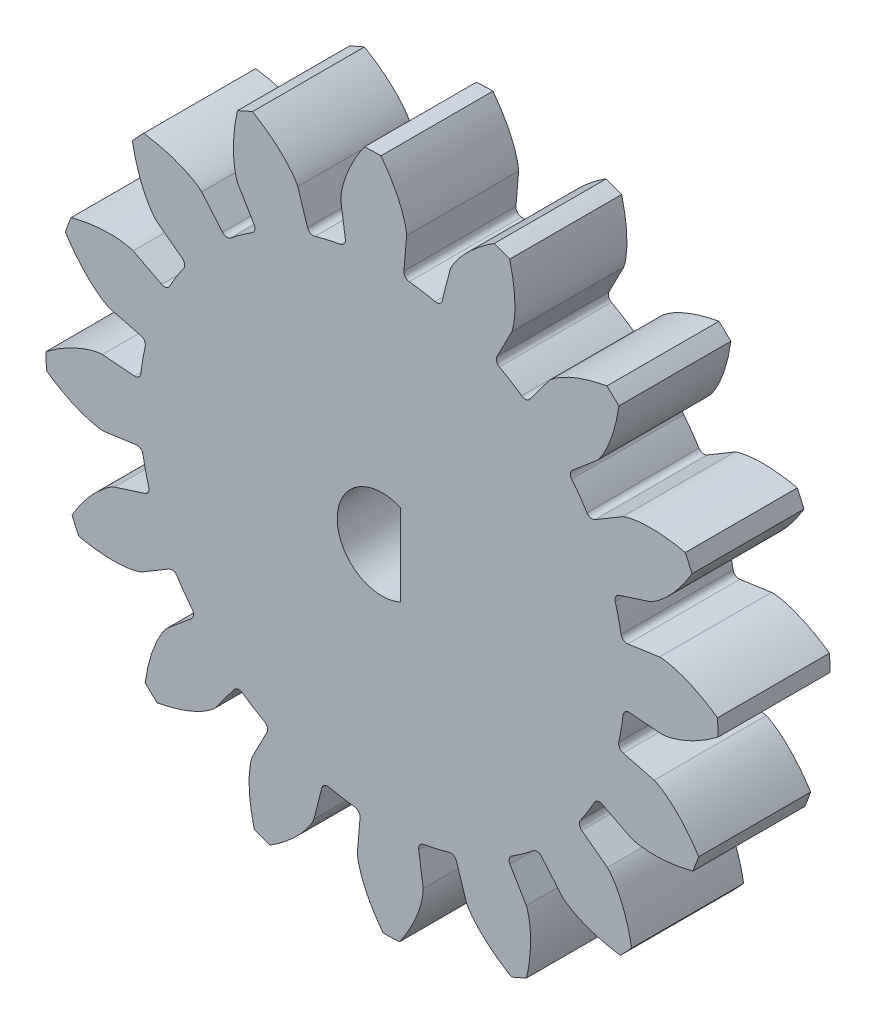
SolidWorks part; units mm, degrees
ref_plane "Front Plane" through (0, 0, 0) normal (0, 0, 1) x (1, 0, 0)
ref_plane "Top Plane" through (0, 0, 0) normal (0, 1, 0) x (1, 0, 0)
ref_plane "Right Plane" through (0, 0, 0) normal (1, 0, 0) x (0, 0, -1)
sketch "Sketch1" plane through (0, 0, 0) normal (0, 0, 1) x (1, 0, 0)
  circle A0 centre (0, 0) radius 28.575
  dimension "D1" = 57.15
extrude "Boss-Extrude1" add sketch "Sketch1" along normal blind 9.525
sketch "Sketch2" plane through (0, 0, 0) normal (0, 0, 1) x (1, 0, 0)
  line L0 (20.352, -3.4211) -> (28.1796, -4.7369) construction
  line L1 (0, 0) -> (10.2025, 0) construction
  line L2 (28.1796, -4.7369) -> (20.352, -3.4211) construction
  line L3 (23.7762, -2.0935) -> (21.0542, -1.8663)
  line L4 (20.5073, -5.1201) -> (23.1539, -5.7954)
  line L5 (0, 0) -> (23.7762, -2.0935) construction
  line L6 (0, 0) -> (25.3407, -1.7351) construction
  circle A0 centre (0, 0) radius 20.6375 construction
  circle A1 centre (0, 0) radius 23.8682 construction
  circle A2 centre (0, 0) radius 25.4 construction
  circle A3 centre (0, 0) radius 28.575 construction
  arc A4 (20.5072, -2.3155) -> (20.1372, -4.5167) centre (0, 0) cw
  arc A5 (20.5072, -2.3155) -> (21.0542, -1.8663) centre (21.012, -2.3725) cw
  arc A6 (20.1372, -4.5167) -> (20.5073, -5.1201) centre (20.6329, -4.6279) ccw
  arc A7 (28.5749, 0.0858) -> (26.9334, -9.546) centre (0, 0) cw construction
  spline S0 degree 4 poles (23.7762, -2.0935) (23.7849, -2.0935) (23.8091, -2.0932) (23.855, -2.0911) (23.9297, -2.0855) (24.0248, -2.0751) (24.1475, -2.0579) (24.2916, -2.0328) (24.4495, -2.0001) (24.6206, -1.9593) (24.7906, -1.9137) (24.9595, -1.8639) (25.1271, -1.8102) (25.3292, -1.7406) (25.5702, -1.6505) (25.8499, -1.5359) (26.1645, -1.3949) (26.4821, -1.2395) (26.7919, -1.0769) (27.1016, -0.9018) (27.3989, -0.7247) (27.7039, -0.5297) (27.9837, -0.3441) (28.2926, -0.1242) (28.5406, 0.0568) (28.8628, 0.3082) (29.0516, 0.4604) (29.2707, 0.6429) (29.367, 0.7262) (29.4263, 0.7774) knots 0 0 0 0 0 0.005377 0.015084 0.028532 0.04661 0.064855 0.092111 0.119476 0.146842 0.174209 0.201575 0.228941 0.256307 0.307035 0.361767 0.4165 0.471232 0.525964 0.580697 0.635429 0.690161 0.744894 0.799626 0.854358 0.909091 0.954545 1 1 1 1 1 construction
  spline S1 degree 4 poles (23.7762, -2.0935) (23.7849, -2.0935) (23.8091, -2.0932) (23.855, -2.0911) (23.9297, -2.0855) (24.0248, -2.0751) (24.1475, -2.0579) (24.2916, -2.0328) (24.4495, -2.0001) (24.6206, -1.9593) (24.7906, -1.9137) (24.9595, -1.8639) (25.1271, -1.8102) (25.3292, -1.7406) (25.5702, -1.6505) (25.8499, -1.5359) (26.1645, -1.3949) (26.4821, -1.2395) (26.7919, -1.0769) (27.1016, -0.9018) (27.3989, -0.7247) (27.7039, -0.5297) (27.9837, -0.3441) (28.2926, -0.1242) (28.5406, 0.0568) (28.793, 0.2537) (28.9152, 0.351) (28.9774, 0.4013) knots 0 0 0 0 0 0.005377 0.015084 0.028532 0.04661 0.064855 0.092111 0.119476 0.146842 0.174209 0.201575 0.228941 0.256307 0.307035 0.361767 0.4165 0.471232 0.525964 0.580697 0.635429 0.690161 0.744894 0.799626 0.854358 0.909091 0.909091 0.909091 0.909091 0.909091
  spline S2 degree 4 poles (23.1539, -5.7954) (23.162, -5.7983) (23.1847, -5.807) (23.227, -5.8248) (23.2952, -5.8559) (23.3808, -5.8986) (23.49, -5.9571) (23.6166, -6.0305) (23.7534, -6.1157) (23.8998, -6.2132) (24.0436, -6.3147) (24.1849, -6.4198) (24.3236, -6.5281) (24.4892, -6.6633) (24.6843, -6.8311) (24.9071, -7.0354) (25.1536, -7.2764) (25.3978, -7.532) (25.6323, -7.7916) (25.8624, -8.063) (26.0802, -8.332) (26.299, -8.6204) (26.4974, -8.8912) (26.7112, -9.2044) (26.8814, -9.46) (27.0968, -9.8072) (27.2214, -10.0153) (27.3639, -10.2623) (27.4255, -10.3737) (27.4635, -10.4423) knots 0 0 0 0 0 0.005377 0.015084 0.028532 0.04661 0.064855 0.092111 0.119476 0.146842 0.174209 0.201575 0.228941 0.256307 0.307035 0.361767 0.4165 0.471232 0.525964 0.580697 0.635429 0.690161 0.744894 0.799626 0.854358 0.909091 0.954545 1 1 1 1 1 construction
  spline S3 degree 4 poles (23.1539, -5.7954) (23.162, -5.7983) (23.1847, -5.807) (23.227, -5.8248) (23.2952, -5.8559) (23.3808, -5.8986) (23.49, -5.9571) (23.6166, -6.0305) (23.7534, -6.1157) (23.8998, -6.2132) (24.0436, -6.3147) (24.1849, -6.4198) (24.3236, -6.5281) (24.4892, -6.6633) (24.6843, -6.8311) (24.9071, -7.0354) (25.1536, -7.2764) (25.3978, -7.532) (25.6323, -7.7916) (25.8624, -8.063) (26.0802, -8.332) (26.299, -8.6204) (26.4974, -8.8912) (26.7112, -9.2044) (26.8814, -9.46) (27.0501, -9.732) (27.1312, -9.8655) (27.1722, -9.9342) knots 0 0 0 0 0 0.005377 0.015084 0.028532 0.04661 0.064855 0.092111 0.119476 0.146842 0.174209 0.201575 0.228941 0.256307 0.307035 0.361767 0.4165 0.471232 0.525964 0.580697 0.635429 0.690161 0.744894 0.799626 0.854358 0.909091 0.909091 0.909091 0.909091 0.909091
  point P21 (20.352, -3.4211)
  dimension "D1" = 50.8
  dimension "D2" = 47.7364
  dimension "D3" = 41.275
  dimension "D6" = 0.508
  dimension "D4" = 9.542
  dimension "D5" = 4.771
  dimension "D7" = 4.771
  dimension "D8" = 5.625
extrude "Cut-Extrude3" cut sketch "Sketch2" against normal through all and the other way through all contours S3 L4 A6 A4 A5 L3 S1
pattern_circular "CirPattern1" count 16 over 360 about axis through (0, 0, 9.525) along (0, 0, 1) of "Cut-Extrude3"
sketch "Sketch3" plane through (0, 0, 9.525) normal (0, 0, 1) x (1, 0, 0)
  line L0 (1.5875, 3.4635) -> (1.5875, -3.4635)
  arc A0 (1.5875, 3.4635) -> (1.5875, -3.4635) centre (0, 0) ccw
  arc A1 (1.5875, -3.4635) -> (1.5875, 3.4635) centre (0, 0) ccw construction
  dimension "D1" = 7.62
  dimension "D2" = 1.5875
extrude "Cut-Extrude4" cut sketch "Sketch3" against normal through all
sketch "Sketch4" plane through (0, 0, 9.525) normal (0, 0, 1) x (1, 0, 0)
  line L0 (1.5875, 3.4635) -> (1.5875, -3.4635)
  circle A0 centre (0, 0) radius 3.81 construction
  arc A1 (1.5875, 3.4635) -> (1.5875, -3.4635) centre (0, 0) cw
  dimension "D1" = 1.5875
equation "\"p\"= 8'Diametral Pitch"
equation "\"N\"= 16'Number of teeth"
equation "\"Phi\"= 20deg'Pressure angle"
equation "\"a\"= 1 / \"p\"'Addendum"
equation "\"b\"= 1.5 / \"p\"'Dedendum"
equation "\"dp\"= \"N\" / \"p\"'Pitch cirlce diameter"
equation "\"db\"= \"dp\" * cos ( \"Phi\" )'Base circle diameter"
equation "\"c\"= \"b\" - \"a\"'Clearance"
equation "\"alpha\"= sqr ( \"dp\" ^ 2 - \"db\" ^ 2 ) / \"db\" * 180 / pi - \"Phi\""
equation "\"D1@Sketch1\"=\"dp\" + 2 * \"a\""
equation "\"D1@Sketch2\"=\"dp\""
equation "\"D2@Sketch2\"=\"db\""
equation "\"D3@Sketch2\"=\"dp\"-2*\"b\""
equation "\"beta\"= ( 360 / ( 4 * \"N\" ) - \"alpha\" ) * 2"
equation "\"D4@Sketch2\"=\"beta\""
equation "\"D5@Sketch2\"=\"D4@Sketch2\"/2"
equation "\"D1@CirPattern1\"=\"N\""
equation "\"D7@Sketch2\"=\"D5@Sketch2\""
equation "\"D8@Sketch2\"=360/(4*\"N\")"
equation "\"face\"= .375"
equation "\"D1@Boss-Extrude1\"=\"face\""
equation "\"bore\"= .3"
equation "\"D1@Sketch3\"=\"bore\""
